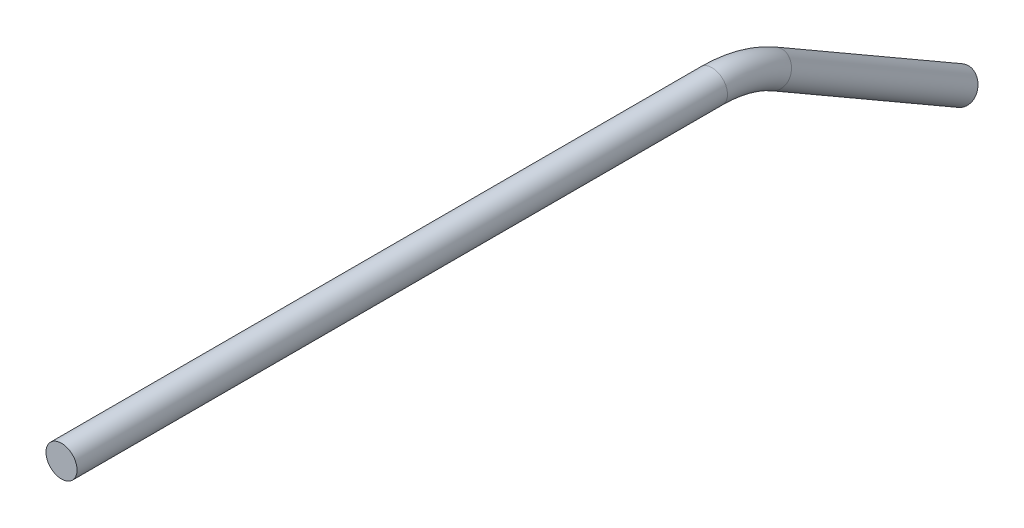
SolidWorks part; units mm, degrees
ref_plane "Front Plane" through (0, 0, 0) normal (0, 0, 1) x (1, 0, 0)
ref_plane "Top Plane" through (0, 0, 0) normal (0, 1, 0) x (1, 0, 0)
ref_plane "Right Plane" through (0, 0, 0) normal (1, 0, 0) x (0, 0, -1)
sketch "Sketch2" plane through (0, 0, 0) normal (0, 0, 1) x (1, 0, 0)
  circle A0 centre (0, 0) radius 3.175
  dimension "D1" = 6.35
sketch "Sketch4" plane through (0, 0, 0) normal (1, 0, 0) x (0, 0, -1)
  line L0 (0, 0) -> (132.8941, 0)
  line L1 (145.5941, -3.403) -> (183.6941, -25.4)
  arc A0 (145.5941, -3.403) -> (132.8941, 0) centre (132.8941, -25.4) ccw
  point P6 (139.7, 0)
  dimension "D4" = 25.4
  dimension "D1" = 139.7
  dimension "D2" = 50.8
  dimension "D3" = 30
sweep "Sweep1" add profiles "Sketch2" path "Sketch4"
